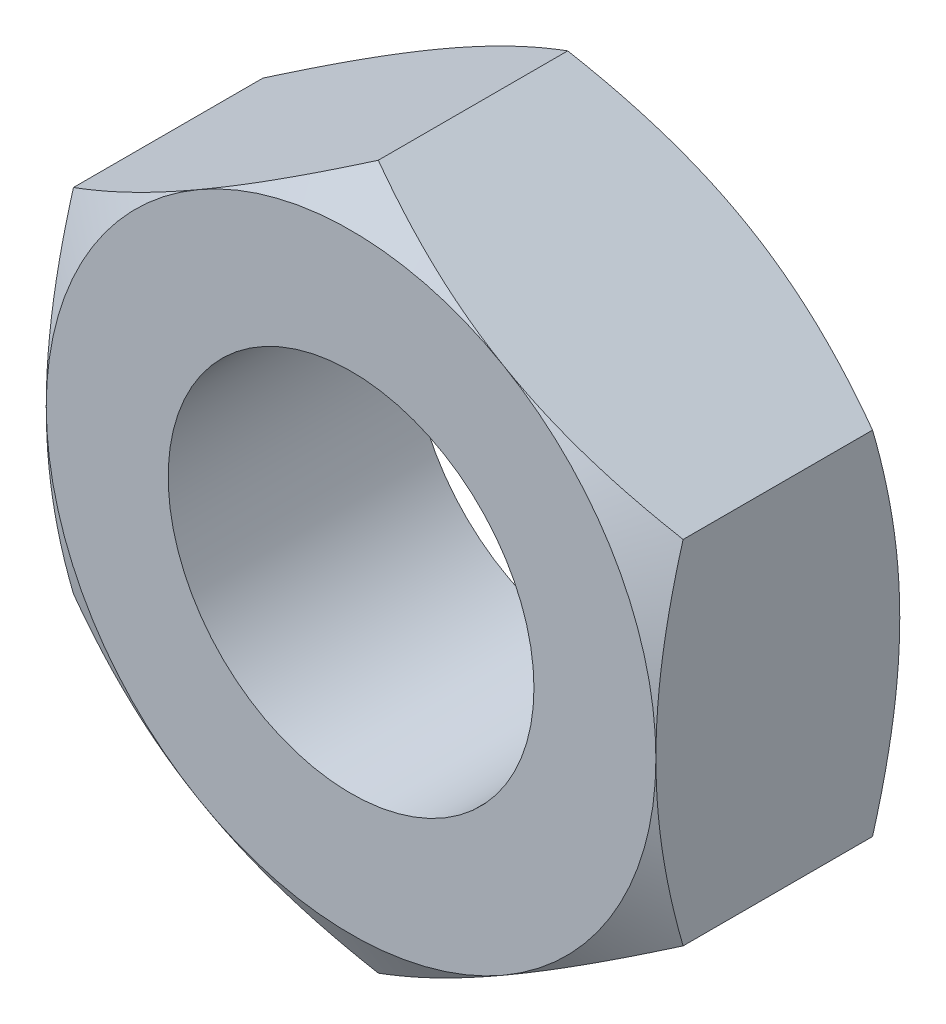
SolidWorks part; units mm, degrees
material "1.4000 (X6Cr13)"
ref_plane "Płaszczyzna XY" through (0, 0, 0) normal (0, 0, 1) x (1, 0, 0)
ref_plane "Płaszczyzna XZ" through (0, 0, 0) normal (0, 1, 0) x (1, 0, 0)
ref_plane "Płaszczyzna YZ" through (0, 0, 0) normal (1, 0, 0) x (0, 0, -1)
sketch "Szkic1" plane through (0, 0, 0) normal (0, 0, 1) x (1, 0, 0)
  line L1 (5, 2.8868) -> (0, 5.7735)
  line L2 (0, 5.7735) -> (-5, 2.8868)
  line L3 (-5, 2.8868) -> (-5, -2.8868)
  line L4 (-5, -2.8868) -> (0, -5.7735)
  line L5 (0, -5.7735) -> (5, -2.8868)
  line L6 (5, -2.8868) -> (5, 2.8868)
  circle A0 centre (0, 0) radius 5 construction
  circle A1 centre (0, 0) radius 3
  dimension "D2" = 6
  dimension "D1" = 10
extrude "Dodanie-wyciągnięcie1" add sketch "Szkic1" along normal blind 4
sketch "Szkic2" plane through (0, 0, 0) normal (0, 1, 0) x (1, 0, 0)
  line L0 (-5, -4) -> (-5, 0)
  line L1 (-5, -4) -> (-5, 0) construction
  line L2 (3, 0) -> (3, -4)
  line L3 (-3, -4) -> (-3, 0)
  line L5 (3, 0) -> (3, -4)
  line L6 (-5, -4) -> (-8.4641, -2)
  line L7 (-5, -4) -> (-3, -4)
  line L8 (-8.4641, -2) -> (-5, 0)
  line L9 (0, -9.8911) -> (0, 0.9366) construction
  line L11 (-5, -4) -> (-8.4641, -4)
  line L13 (-5, 0) -> (-8.4641, 0)
  line L14 (-8.4641, -4) -> (-8.4641, 0)
  dimension "D1" = 30
  dimension "D2" = 60
revolve "Wycięcie-obrót1" cut sketch "Szkic2" angle 360 about L9
